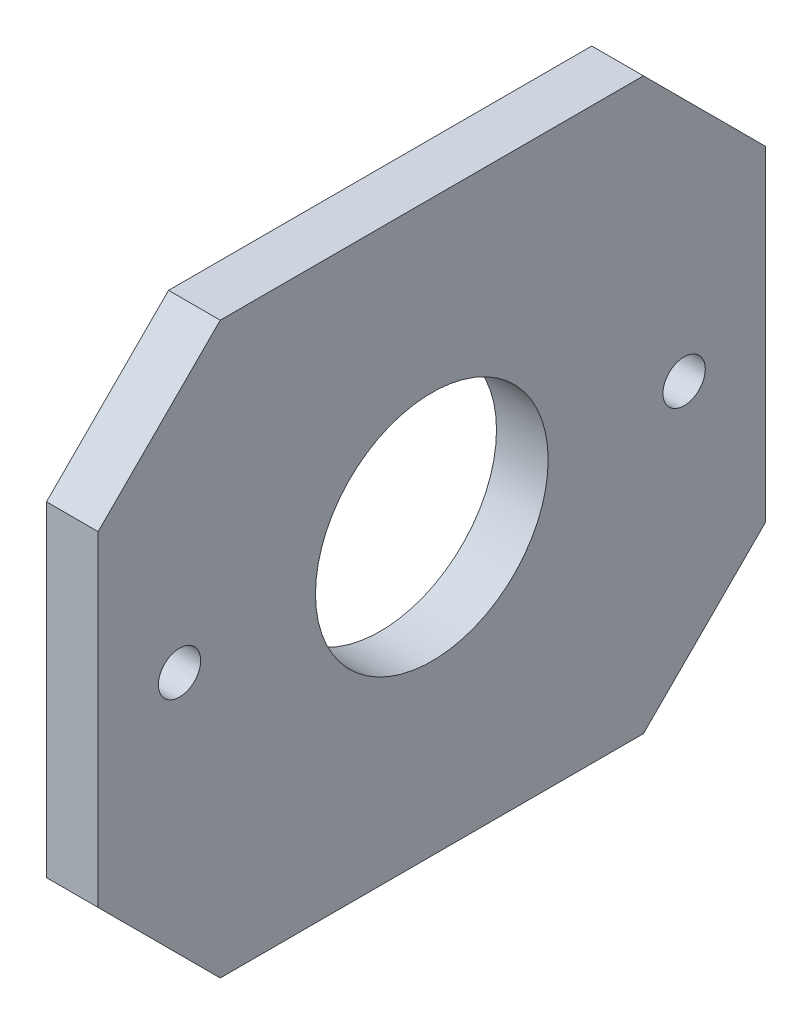
SolidWorks part; units mm, degrees
ref_plane "Front Plane" through (0, 0, 0) normal (0, 0, 1) x (1, 0, 0)
ref_plane "Top Plane" through (0, 0, 0) normal (0, 1, 0) x (1, 0, 0)
ref_plane "Right Plane" through (0, 0, 0) normal (1, 0, 0) x (0, 0, -1)
sketch "Sketch1" plane through (0, 0, 0) normal (1, 0, 0) x (0, 0, -1)
  line L3 (-41, 0) -> (41, 0) construction
  line L4 (-41, 35) -> (41, 35)
  line L5 (-41, 35) -> (-41, -35)
  line L6 (-41, -35) -> (41, -35)
  line L7 (41, 35) -> (41, -35)
  circle A0 centre (0, 0) radius 14.295
  circle A3 centre (-31, 0) radius 2.6
  circle A4 centre (31, 0) radius 2.6
  point P8 (0, 35)
  dimension "D3" = 28.59
  dimension "D4" = 5.2
  dimension "D5" = 5.2
  dimension "D1" = 82
  dimension "D2" = 70
  dimension "D6" = 10
  dimension "D7" = 10
extrude "Boss-Extrude1" add sketch "Sketch1" along normal blind 6.35
chamfer "Chamfer1" distance 15 angle 45 4 edges at (3.175, 35, -41) (3.175, -35, -41) (3.175, -35, 41) (3.175, 35, 41)
